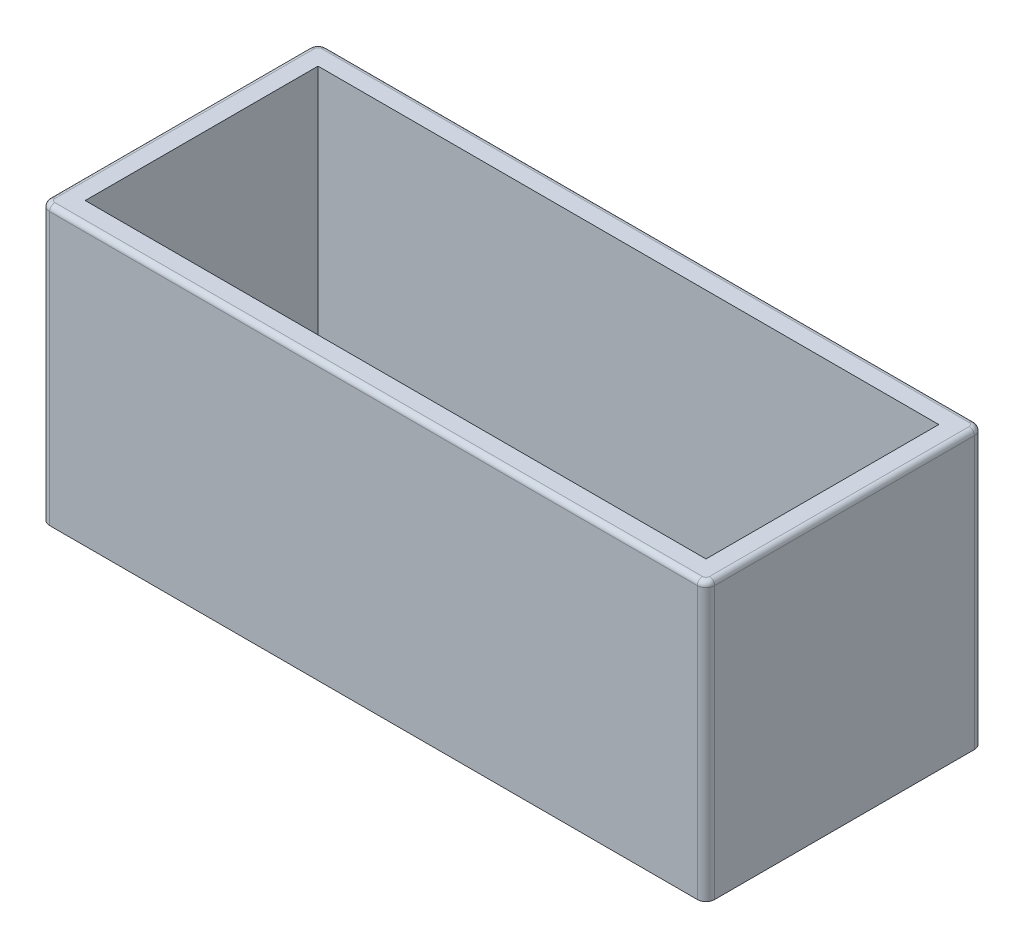
SolidWorks part; units mm, degrees
ref_plane "Front Plane" through (0, 0, 0) normal (0, 0, 1) x (1, 0, 0)
ref_plane "Top Plane" through (0, 0, 0) normal (0, 1, 0) x (1, 0, 0)
ref_plane "Right Plane" through (0, 0, 0) normal (1, 0, 0) x (0, 0, -1)
sketch "Sketch1" plane through (0, 0, 0) normal (1, 0, 0) x (0, 0, -1)
  line L1 (-31.75, -31.75) -> (31.75, -31.75)
  line L2 (-31.75, -31.75) -> (-31.75, 31.75)
  line L3 (-31.75, 31.75) -> (31.75, 31.75)
  line L4 (31.75, -31.75) -> (31.75, 31.75)
  line L5 (-31.75, -31.75) -> (31.75, 31.75) construction
  line L6 (-31.75, 31.75) -> (31.75, -31.75) construction
  point P0 (0, 0)
  dimension "D1" = 63.5
extrude "Boss-Extrude1" add sketch "Sketch1" along normal blind 152.4
sketch "Sketch2" plane through (0, 31.75, 0) normal (0, 1, 0) x (1, 0, 0)
  line L8 (5.08, 26.67) -> (5.08, -26.67)
  line L9 (5.08, -26.67) -> (147.32, -26.67)
  line L10 (147.32, -26.67) -> (147.32, 26.67)
  line L11 (147.32, 26.67) -> (5.08, 26.67)
  line L12 (5.08, 26.67) -> (5.08, -26.67)
  line L13 (5.08, -26.67) -> (147.32, -26.67)
  line L14 (147.32, -26.67) -> (147.32, 26.67)
  line L15 (147.32, 26.67) -> (5.08, 26.67)
  dimension "D1" = 5.08
extrude "Cut-Extrude1" cut sketch "Sketch2" against normal offset from surface (58.42 mm away) 5.08 up to face at (76.2, -31.75, 0)
fillet "Fillet1" radius 2 4 edges at (152.4, 0, 31.75) (152.4, 0, -31.75) (0, 0, -31.75) (0, 0, 31.75)
fillet "Fillet2" radius 1.2 8 edges at (151.8142, 31.75, -31.1642) (152.4, 31.75, 0) (151.8142, 31.75, 31.1642) (76.2, 31.75, 31.75) (0.5858, 31.75, 31.1642) (0, 31.75, 0) (0.5858, 31.75, -31.1642) (76.2, 31.75, -31.75)
scale "Scale1" scale about centroid uniform scaling yes scale factor 0.06
